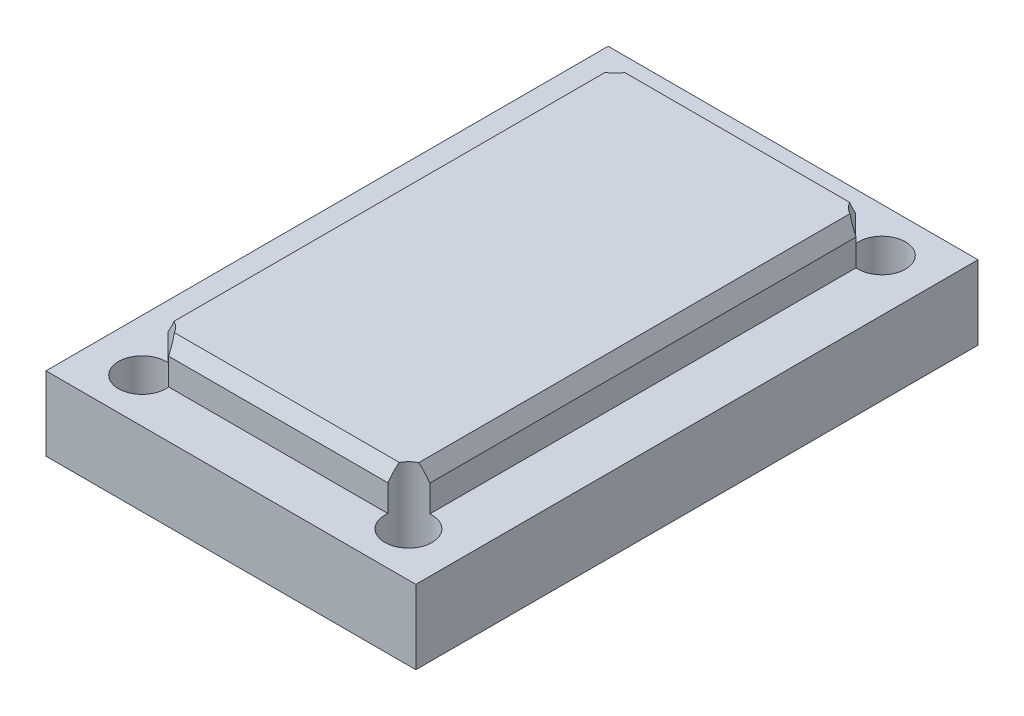
SolidWorks part; units mm, degrees
ref_plane "Спереди" through (0, 0, 0) normal (0, 0, 1) x (1, 0, 0)
ref_plane "Сверху" through (0, 0, 0) normal (0, 1, 0) x (1, 0, 0)
ref_plane "Справа" through (0, 0, 0) normal (1, 0, 0) x (0, 0, -1)
sketch "Sketch1" plane through (0, 0, 0) normal (0, 1, 0) x (1, 0, 0)
  line L1 (12.5, -19) -> (-12.5, -19)
  line L2 (12.5, -19) -> (12.5, 19)
  line L3 (12.5, 19) -> (-12.5, 19)
  line L4 (-12.5, -19) -> (-12.5, 19)
  line L5 (12.5, -19) -> (-12.5, 19) construction
  line L6 (12.5, 19) -> (-12.5, -19) construction
  point P0 (0, 0)
  dimension "D1" = 25
  dimension "D2" = 38
extrude "Boss-Extrude1" add sketch "Sketch1" along normal blind 5
sketch "Sketch4" plane through (0, 5, 0) normal (0, 1, 0) x (1, 0, 0)
  circle A0 centre (0, 0) radius 4.15
  dimension "D1" = 8.3
extrude "Cut-Extrude2" cut sketch "Sketch4" against normal through all
sketch "Sketch9" plane through (0, 5, 0) normal (0, 1, 0) x (1, 0, 0)
  line L1 (8.85, 15.8) -> (-8.85, 15.8)
  line L2 (8.85, 15.8) -> (8.85, -15.8)
  line L3 (8.85, -15.8) -> (-8.85, -15.8)
  line L4 (-8.85, 15.8) -> (-8.85, -15.8)
  line L5 (8.85, 15.8) -> (-8.85, -15.8) construction
  line L6 (8.85, -15.8) -> (-8.85, 15.8) construction
  line L7 (-3.7, -6.4086) -> (3.7, -6.4086) construction
  line L8 (3.7, -6.4086) -> (7.4, 0) construction
  line L9 (7.4, 0) -> (3.7, 6.4086) construction
  line L10 (3.7, 6.4086) -> (-3.7, 6.4086) construction
  line L11 (-3.7, 6.4086) -> (-7.4, 0) construction
  line L12 (-7.4, 0) -> (-3.7, -6.4086) construction
  circle A0 centre (0, 0) radius 7.4 construction
  point P0 (0, 0)
  dimension "D2" = 14.8
  dimension "D1" = 17.7
  dimension "D3" = 31.6
extrude "Boss-Extrude3" add sketch "Sketch9" along normal blind 2.8
sketch "Sketch6" plane through (0, 5, 0) normal (0, 1, 0) x (1, 0, 0)
  line L1 (-9, 16) -> (9, 16) construction
  line L2 (-9, 16) -> (-9, -16) construction
  line L3 (-9, -16) -> (9, -16) construction
  line L4 (9, 16) -> (9, -16) construction
  line L5 (-9, 16) -> (9, -16) construction
  line L6 (-9, -16) -> (9, 16) construction
  circle A0 centre (9, -16) radius 1.6
  circle A1 centre (-9, -16) radius 1.6
  circle A2 centre (-9, 16) radius 1.6
  circle A3 centre (9, 16) radius 1.6
  point P0 (0, 0)
  dimension "D1" = 3.2
  dimension "D2" = 18
  dimension "D3" = 32
extrude "Cut-Extrude4" cut sketch "Sketch6" against normal through all both and the other way through all
chamfer "Chamfer1" distance 1 angle 30 4 edges at (8.85, 7.8, 0) (0, 7.8, -15.8) (-8.85, 7.8, 0) (0, 7.8, 15.8)
sketch "Sketch10" plane through (0, 5, 0) normal (0, -1, 0) x (1, 0, 0)
  circle A0 centre (0, 0) radius 4.15
extrude "Boss-Extrude4" add sketch "Sketch10" along normal up to surface (5 mm away) up to face at (-9, 0, 17.6)
